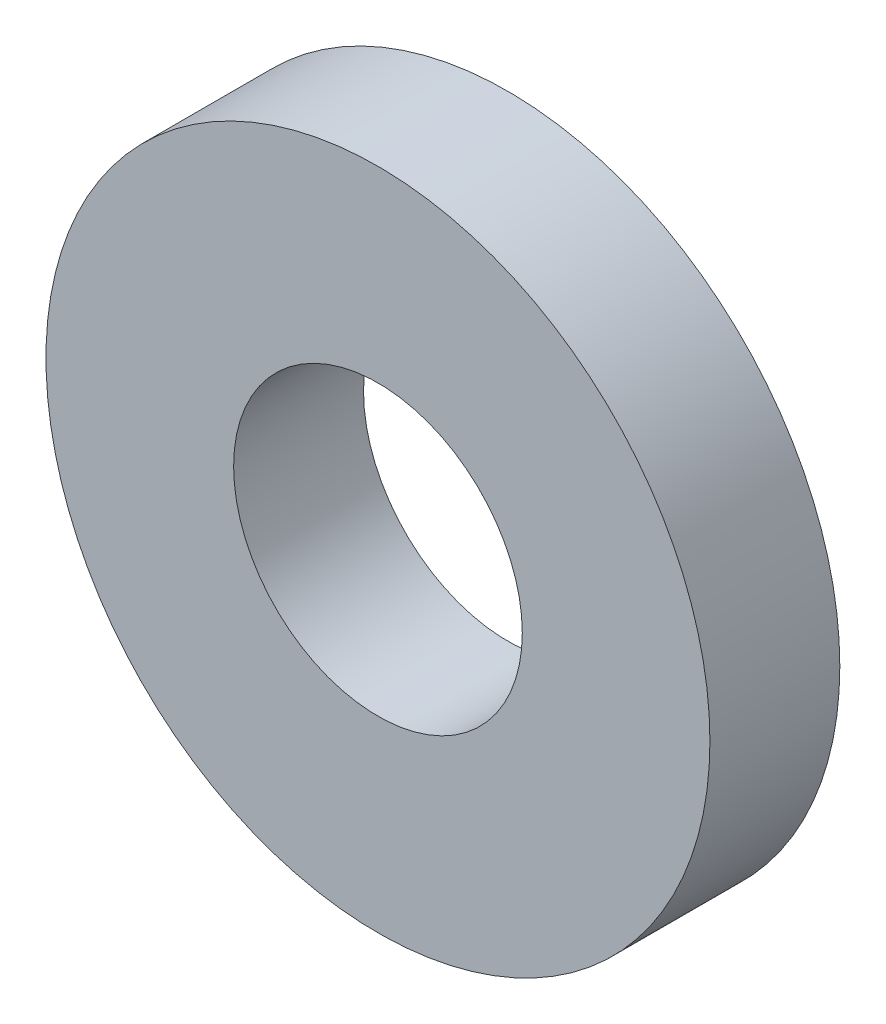
SolidWorks part; units mm, degrees
material "Латунь"
ref_plane "Спереди" through (0, 0, 0) normal (0, 0, 1) x (1, 0, 0)
ref_plane "Сверху" through (0, 0, 0) normal (0, 1, 0) x (1, 0, 0)
ref_plane "Справа" through (0, 0, 0) normal (1, 0, 0) x (0, 0, -1)
sketch "Эскиз1" plane through (0, 0, 0) normal (0, 0, 1) x (1, 0, 0)
  circle A0 centre (0, 0) radius 10
  circle A1 centre (0, 0) radius 23
  dimension "D1" = 20
  dimension "D2" = 46
extrude "Бобышка-Вытянуть1" add sketch "Эскиз1" along normal blind 9
